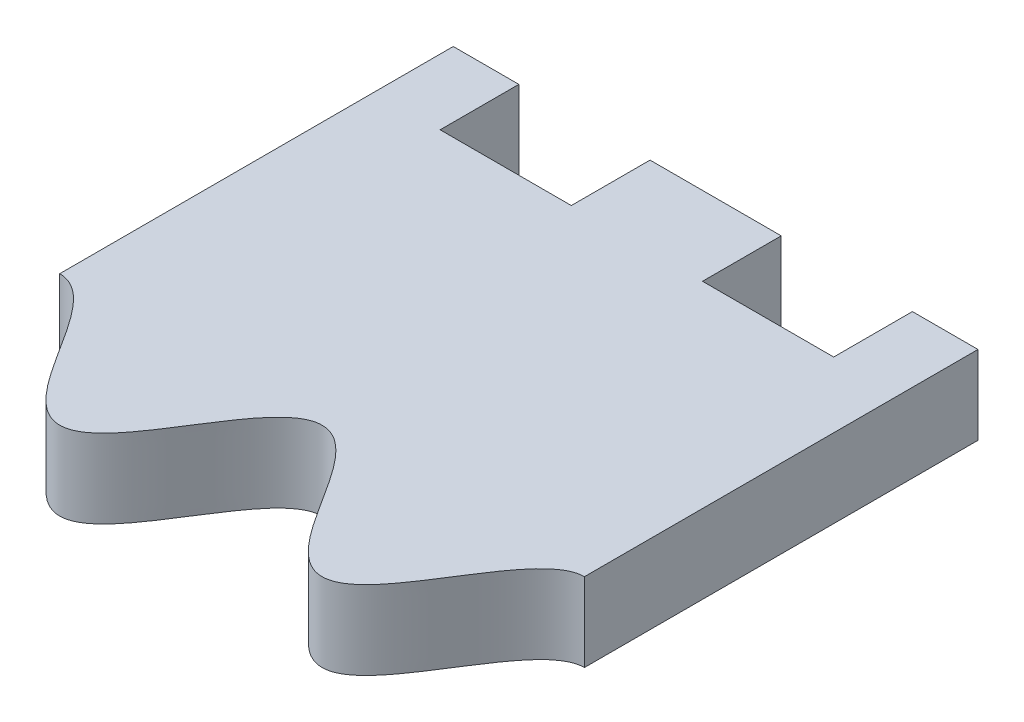
SolidWorks part; units mm, degrees
ref_plane "Front Plane" through (0, 0, 0) normal (0, 0, 1) x (1, 0, 0)
ref_plane "Top Plane" through (0, 0, 0) normal (0, 1, 0) x (1, 0, 0)
ref_plane "Right Plane" through (0, 0, 0) normal (1, 0, 0) x (0, 0, -1)
sketch "Sketch1" plane through (0, 0, 0) normal (0, 1, 0) x (1, 0, 0)
  line L1 (-10, -10) -> (10, -10)
  line L2 (-10, -10) -> (-10, 10)
  line L3 (-10, 10) -> (10, 10)
  line L4 (10, -10) -> (10, 10)
  line L5 (-10, -10) -> (10, 10) construction
  line L6 (-10, 10) -> (10, -10) construction
  point P0 (0, 0)
  dimension "D1" = 20
  dimension "D2" = 20
extrude "Boss-Extrude1" add sketch "Sketch1" along normal blind 3
sketch "Sketch2" plane through (0, 3, 0) normal (0, 1, 0) x (1, 0, 0)
  line L1 (-10, 10) -> (-10, -10) construction
  line L6 (10, -10) -> (10, 10) construction
  line L7 (10, -5) -> (10, -10)
  line L8 (10, -10) -> (-10, -10)
  line L9 (-10, -10) -> (-10, -5)
  spline S0 degree 4 poles (-12, -6.7275) (-11.9654, -6.6757) (-11.8956, -6.5725) (-11.7895, -6.4188) (-11.6438, -6.2167) (-11.4928, -6.0185) (-11.3351, -5.8256) (-11.1688, -5.6399) (-10.9918, -5.4644) (-10.8134, -5.3134) (-10.6529, -5.2028) (-10.5163, -5.1279) (-10.4095, -5.0808) (-10.3218, -5.0493) (-10.2423, -5.0278) (-10.1753, -5.0142) (-10.1162, -5.0062) (-10.0655, -5.002) (-10.0182, -4.9999) (-9.9842, -4.9998) (-9.9394, -5.0017) (-9.892, -5.0055) (-9.8359, -5.0124) (-9.773, -5.0243) (-9.6989, -5.0432) (-9.616, -5.071) (-9.5154, -5.1128) (-9.3873, -5.1789) (-9.2371, -5.2764) (-9.07, -5.4098) (-8.9046, -5.5651) (-8.749, -5.7301) (-8.6013, -5.9021) (-8.4601, -6.0795) (-8.324, -6.2608) (-8.1827, -6.4585) (-8.0359, -6.6724) (-7.8835, -6.9022) (-7.7248, -7.1474) (-7.5284, -7.4551) (-7.2936, -7.825) (-7.0346, -8.2261) (-6.743, -8.6525) (-6.4528, -9.0386) (-6.1598, -9.3795) (-5.8517, -9.6694) (-5.521, -9.8895) (-5.1672, -10.0108) (-4.8167, -10.0082) (-4.4632, -9.8815) (-4.1325, -9.6563) (-3.8252, -9.3634) (-3.5336, -9.0214) (-3.2446, -8.635) (-2.9542, -8.2091) (-2.6569, -7.748) (-2.3458, -7.2563) (-2.0486, -6.7951) (-1.7583, -6.3691) (-1.4695, -5.9825) (-1.1782, -5.6403) (-0.8714, -5.3469) (-0.5412, -5.1209) (-0.1883, -4.9928) (0.1621, -4.9883) (0.5165, -5.1081) (0.8478, -5.3274) (1.1563, -5.6169) (1.4496, -5.9574) (1.7401, -6.3434) (2.0319, -6.7697) (2.4096, -7.3549) (2.7809, -7.9452) (3.1457, -8.5013) (3.5233, -9.0086) (3.8169, -9.3546) (4.126, -9.6513) (4.459, -9.8796) (4.8145, -10.0081) (5.1665, -10.011) (5.521, -9.8895) (5.8517, -9.6694) (6.1598, -9.3794) (6.4528, -9.0387) (6.743, -8.6525) (7.0346, -8.2261) (7.3332, -7.7637) (7.6064, -7.3317) (7.8431, -6.963) (8.0359, -6.6724) (8.1827, -6.4585) (8.324, -6.2608) (8.4601, -6.0795) (8.6013, -5.9021) (8.749, -5.7301) (8.9046, -5.5651) (9.07, -5.4098) (9.2371, -5.2764) (9.4057, -5.167) (9.5545, -5.0935) (9.6777, -5.0486) (9.773, -5.0243) (9.8359, -5.0124) (9.892, -5.0055) (9.9394, -5.0017) (9.9842, -4.9998) (10.0182, -4.9999) (10.0655, -5.002) (10.1162, -5.0062) (10.1753, -5.0142) (10.2423, -5.0278) (10.3218, -5.0493) (10.4095, -5.0808) (10.5163, -5.1279) (10.6529, -5.2028) (10.8134, -5.3134) (10.9918, -5.4644) (11.1467, -5.618) (11.2727, -5.756) (11.374, -5.8743) (11.4529, -5.9706) (11.5494, -6.0928) (11.662, -6.2419) (11.7895, -6.4188) (11.8956, -6.5725) (11.9654, -6.6757) (12, -6.7275) knots 0 0 0 0 0 0.007168 0.014336 0.021504 0.028672 0.03584 0.043008 0.050176 0.057345 0.062712 0.065396 0.06808 0.070764 0.073448 0.07479 0.076132 0.077474 0.078815 0.08007 0.081324 0.082579 0.083833 0.086342 0.08885 0.091359 0.093868 0.098885 0.105408 0.111931 0.118454 0.124976 0.131499 0.138022 0.144545 0.151068 0.159472 0.167876 0.176281 0.184685 0.201494 0.218303 0.231224 0.244144 0.257065 0.269985 0.279769 0.289552 0.299506 0.309461 0.322382 0.335304 0.348225 0.361147 0.377889 0.394632 0.411374 0.428117 0.441039 0.45396 0.466882 0.479803 0.489758 0.499712 0.509495 0.519278 0.532199 0.54512 0.55804 0.570961 0.587769 0.604578 0.638196 0.651242 0.664287 0.677333 0.690379 0.700413 0.710448 0.720231 0.730015 0.742935 0.755856 0.768776 0.781697 0.798506 0.815315 0.832124 0.840528 0.848932 0.855455 0.861978 0.868501 0.875024 0.881546 0.888069 0.894592 0.901115 0.906132 0.91115 0.913658 0.916167 0.917421 0.918676 0.91993 0.921185 0.922526 0.923868 0.92521 0.926552 0.929236 0.93192 0.934604 0.937288 0.942655 0.949824 0.956992 0.96416 0.967744 0.971328 0.974912 0.978496 0.985664 0.992832 1 1 1 1 1 construction
  spline S1 degree 4 poles (-10, -5) (-9.9908, -5) (-9.9724, -5.0003) (-9.9394, -5.0017) (-9.892, -5.0055) (-9.8359, -5.0124) (-9.773, -5.0243) (-9.6989, -5.0432) (-9.616, -5.071) (-9.5154, -5.1128) (-9.3873, -5.1789) (-9.2371, -5.2764) (-9.07, -5.4098) (-8.9046, -5.5651) (-8.749, -5.7301) (-8.6013, -5.9021) (-8.4601, -6.0795) (-8.324, -6.2608) (-8.1827, -6.4585) (-8.0359, -6.6724) (-7.8835, -6.9022) (-7.7248, -7.1474) (-7.5284, -7.4551) (-7.2936, -7.825) (-7.0346, -8.2261) (-6.743, -8.6525) (-6.4528, -9.0386) (-6.1598, -9.3795) (-5.8517, -9.6694) (-5.521, -9.8895) (-5.1672, -10.0108) (-4.8167, -10.0082) (-4.4632, -9.8815) (-4.1325, -9.6563) (-3.8252, -9.3634) (-3.5336, -9.0214) (-3.2446, -8.635) (-2.9542, -8.2091) (-2.6569, -7.748) (-2.3458, -7.2563) (-2.0486, -6.7951) (-1.7583, -6.3691) (-1.4695, -5.9825) (-1.1782, -5.6403) (-0.8714, -5.3469) (-0.5412, -5.1209) (-0.1883, -4.9928) (0.1621, -4.9883) (0.5165, -5.1081) (0.8478, -5.3274) (1.1563, -5.6169) (1.4496, -5.9574) (1.7401, -6.3434) (2.0319, -6.7697) (2.4096, -7.3549) (2.7809, -7.9452) (3.1457, -8.5013) (3.5233, -9.0086) (3.8169, -9.3546) (4.126, -9.6513) (4.459, -9.8796) (4.8145, -10.0081) (5.1665, -10.011) (5.521, -9.8895) (5.8517, -9.6694) (6.1598, -9.3794) (6.4528, -9.0387) (6.743, -8.6525) (7.0346, -8.2261) (7.3332, -7.7637) (7.6064, -7.3317) (7.8431, -6.963) (8.0359, -6.6724) (8.1827, -6.4585) (8.324, -6.2608) (8.4601, -6.0795) (8.6013, -5.9021) (8.749, -5.7301) (8.9046, -5.5651) (9.07, -5.4098) (9.2371, -5.2764) (9.4057, -5.167) (9.5545, -5.0935) (9.6777, -5.0486) (9.773, -5.0243) (9.8359, -5.0124) (9.892, -5.0055) (9.9394, -5.0017) (9.9724, -5.0003) (9.9908, -5) (10, -5) knots 0.078815 0.078815 0.078815 0.078815 0.078815 0.08007 0.081324 0.082579 0.083833 0.086342 0.08885 0.091359 0.093868 0.098885 0.105408 0.111931 0.118454 0.124976 0.131499 0.138022 0.144545 0.151068 0.159472 0.167876 0.176281 0.184685 0.201494 0.218303 0.231224 0.244144 0.257065 0.269985 0.279769 0.289552 0.299506 0.309461 0.322382 0.335304 0.348225 0.361147 0.377889 0.394632 0.411374 0.428117 0.441039 0.45396 0.466882 0.479803 0.489758 0.499712 0.509495 0.519278 0.532199 0.54512 0.55804 0.570961 0.587769 0.604578 0.638196 0.651242 0.664287 0.677333 0.690379 0.700413 0.710448 0.720231 0.730015 0.742935 0.755856 0.768776 0.781697 0.798506 0.815315 0.832124 0.840528 0.848932 0.855455 0.861978 0.868501 0.875024 0.881546 0.888069 0.894592 0.901115 0.906132 0.91115 0.913658 0.916167 0.917421 0.918676 0.91993 0.921185 0.921185 0.921185 0.921185 0.921185
  point P7 (0, 0)
  line M1 (10, -10) -> (10, 10)
  line M3 (-10, 10) -> (-10, -10)
  line M4 (-10, -10) -> (10, -10)
  dimension "D3" = 5
extrude "Cut-Extrude1" cut sketch "Sketch2" against normal through all both and the other way through all contours S1 M3 M4 M1
sketch "Sketch3" plane through (0, 3, 0) normal (0, 1, 0) x (1, 0, 0)
  line L0 (10, 10) -> (-10, 10) construction
  line L1 (-7.5, 10) -> (-2.5, 10)
  line L2 (-7.5, 10) -> (-7.5, 7)
  line L3 (-7.5, 7) -> (-2.5, 7)
  line L4 (-2.5, 10) -> (-2.5, 7)
  line L5 (-10, 10) -> (-10, -5) construction
  dimension "D1" = 3
  dimension "D2" = 5
  dimension "D3" = 2.5
extrude "Cut-Extrude2" cut sketch "Sketch3" against normal through all both and the other way through all
mirror "Mirror1" about plane through (0, 0, 0) normal (1, 0, 0) of "Cut-Extrude2"
